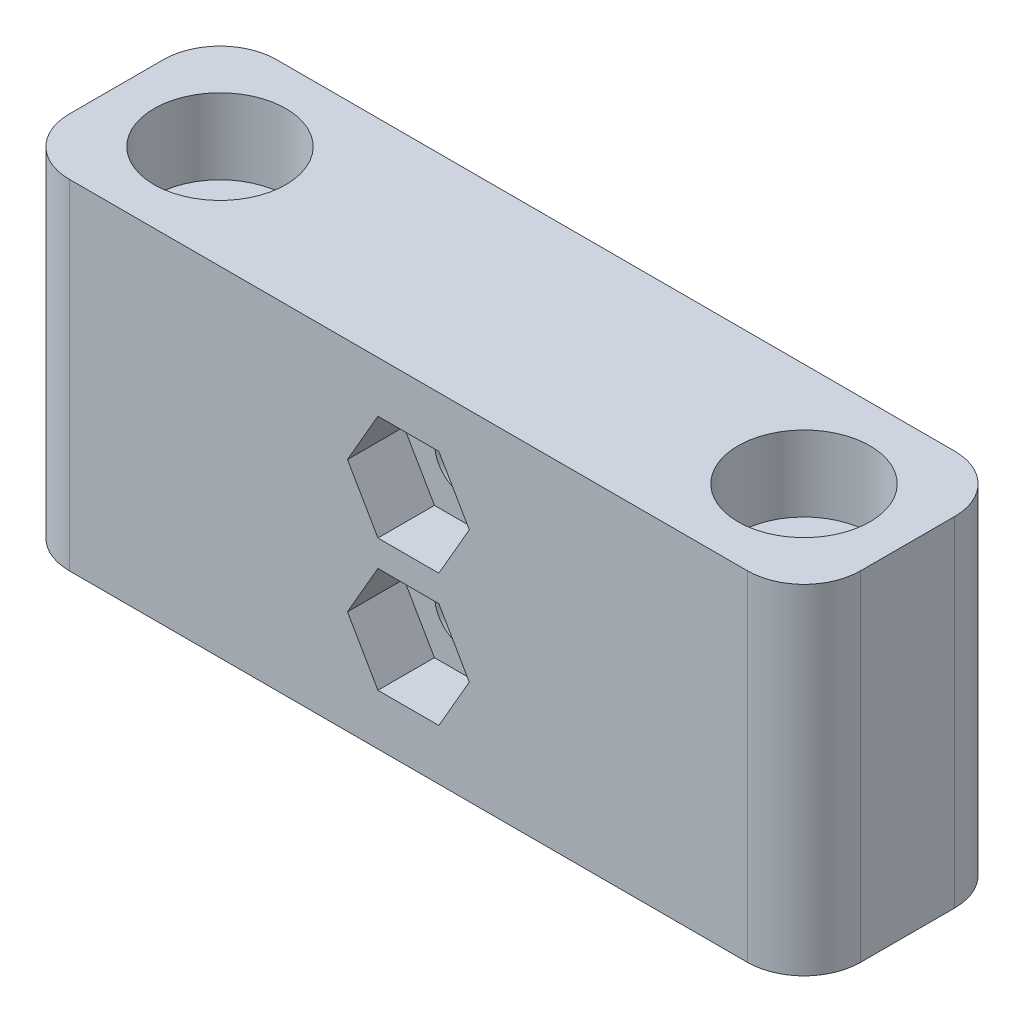
SolidWorks part; units mm, degrees
ref_plane "정면" through (0, 0, 0) normal (0, 0, 1) x (1, 0, 0)
ref_plane "윗면" through (0, 0, 0) normal (0, 1, 0) x (1, 0, 0)
ref_plane "우측면" through (0, 0, 0) normal (1, 0, 0) x (0, 0, -1)
sketch "스케치1" plane through (0, -13.7492, 0) normal (0, 1, 0) x (1, 0, 0)
  line L4 (-32.1558, -58.8025) -> (-32.1558, -24.8025) construction
  line L6 (-32.1558, -51.8025) -> (9.8442, -51.8025)
  line L7 (-32.1558, -51.8025) -> (-32.1558, -62.8025)
  line L8 (-32.1558, -62.8025) -> (9.8442, -62.8025)
  line L9 (9.8442, -51.8025) -> (9.8442, -62.8025)
  circle A0 centre (-26.6558, -57.3025) radius 1.6
  circle A1 centre (4.3442, -57.3025) radius 1.6
  point P13 (-32.1558, -57.3025)
  dimension "D1" = 3.2
  dimension "D2" = 3.2
  dimension "D3" = 0
extrude "보스-돌출1" add sketch "스케치1" along normal blind 18
fillet "필렛1" radius 3 4 edges at (9.8442, -4.7492, 62.8025) (9.8442, -4.7492, 51.8025) (-32.1558, -4.7492, 62.8025) (-32.1558, -4.7492, 51.8025)
sketch "스케치3" plane through (0, 4.2508, 0) normal (0, 1, 0) x (1, 0, 0)
  circle A0 centre (-26.6558, -57.3025) radius 3.5
  circle A1 centre (4.3442, -57.3025) radius 3.5
  dimension "D1" = 7
  dimension "D2" = 7
extrude "컷-돌출2" cut sketch "스케치3" against normal blind 4
sketch "스케치4" plane through (0, 0, 51.8025) normal (0, 0, -1) x (-1, 0, 0)
  line L0 (-6.8442, -4.7492) -> (29.1558, -4.7492)
  line L1 (-6.8442, 4.2508) -> (-6.8442, -13.7492) construction
  line L2 (29.1558, -13.7492) -> (29.1558, 4.2508) construction
  line L3 (11.1558, -1.2492) -> (11.1558, -8.2492)
  circle A0 centre (11.1558, -1.2492) radius 1.6
  circle A1 centre (11.1558, -8.2492) radius 1.6
  point P13 (11.1558, -4.7492)
  dimension "D1" = 7
extrude "컷-돌출3" cut sketch "스케치4" against normal up to vertex (11 mm away)
sketch "스케치6" plane through (0, 0, 62.8025) normal (0, 0, 1) x (1, 0, 0)
  line L1 (-7.9226, -1.2492) -> (-9.5392, 1.5508)
  line L2 (-9.5392, 1.5508) -> (-12.7723, 1.5508)
  line L3 (-12.7723, 1.5508) -> (-14.3889, -1.2492)
  line L4 (-14.3889, -1.2492) -> (-12.7723, -4.0492)
  line L5 (-12.7723, -4.0492) -> (-9.5392, -4.0492)
  line L6 (-9.5392, -4.0492) -> (-7.9226, -1.2492)
  line L7 (-7.9226, -8.2492) -> (-9.5392, -5.4492)
  line L8 (-9.5392, -5.4492) -> (-12.7723, -5.4492)
  line L9 (-12.7723, -5.4492) -> (-14.3889, -8.2492)
  line L10 (-14.3889, -8.2492) -> (-12.7723, -11.0492)
  line L11 (-12.7723, -11.0492) -> (-9.5392, -11.0492)
  line L12 (-9.5392, -11.0492) -> (-7.9226, -8.2492)
  circle A0 centre (-11.1558, -1.2492) radius 2.8 construction
  circle A1 centre (-11.1558, -8.2492) radius 2.8 construction
  dimension "D1" = 5.6
  dimension "D2" = 5.6
extrude "컷-돌출4" cut sketch "스케치6" against normal blind 3
